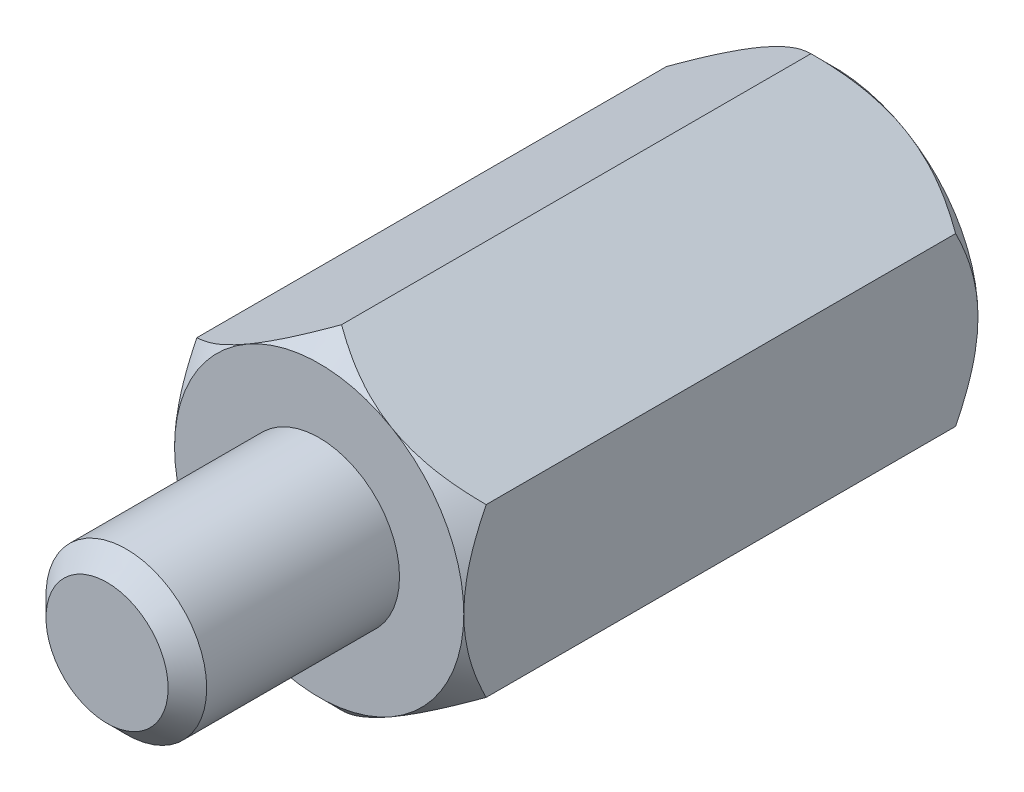
SolidWorks part; units mm, degrees
ref_plane "Front Plane" through (0, 0, 0) normal (0, 0, 1) x (1, 0, 0)
ref_plane "Top Plane" through (0, 0, 0) normal (0, 1, 0) x (1, 0, 0)
ref_plane "Right Plane" through (0, 0, 0) normal (1, 0, 0) x (0, 0, -1)
sketch "Sketch2" plane through (0, 0, 0) normal (0, 0, 1) x (1, 0, 0)
  circle A0 centre (0, 0) radius 1.25
  dimension "D1" = 2.5
extrude "Boss-Extrude1" add sketch "Sketch2" along normal blind 3.3
sketch "Sketch3" plane through (0, 0, 0) normal (0, 0, -1) x (-1, 0, 0)
  line L1 (0, 2.5981) -> (-2.25, 1.299)
  line L2 (-2.25, 1.299) -> (-2.25, -1.299)
  line L3 (-2.25, -1.299) -> (0, -2.5981)
  line L4 (0, -2.5981) -> (2.25, -1.299)
  line L5 (2.25, -1.299) -> (2.25, 1.299)
  line L6 (2.25, 1.299) -> (0, 2.5981)
  circle A0 centre (0, 0) radius 2.25 construction
  dimension "D1" = 4.5
extrude "Boss-Extrude2" add sketch "Sketch3" along normal blind 8
sketch "Sketch4" plane through (0, 0, -8) normal (0, 0, -1) x (-1, 0, 0)
  circle A0 centre (0, 0) radius 1.25
  dimension "D1" = 2.5
extrude "Cut-Extrude1" cut sketch "Sketch4" against normal blind 4.8
sketch "Sketch5" plane through (0, 0, -8) normal (0, 0, -1) x (-1, 0, 0)
  circle A0 centre (0, 0) radius 2.25
extrude "Cut-Extrude2" cut sketch "Sketch5" against normal through all draft 45 flip side to cut
sketch "Sketch6" plane through (0, 0, 0) normal (0, 0, 1) x (1, 0, 0)
  circle A0 centre (0, 0) radius 2.25
extrude "Cut-Extrude3" cut sketch "Sketch6" against normal through all draft 45 flip side to cut
chamfer "Chamfer1" distance 0.3 angle 45 1 edges at (1.25, 0, 3.3)
